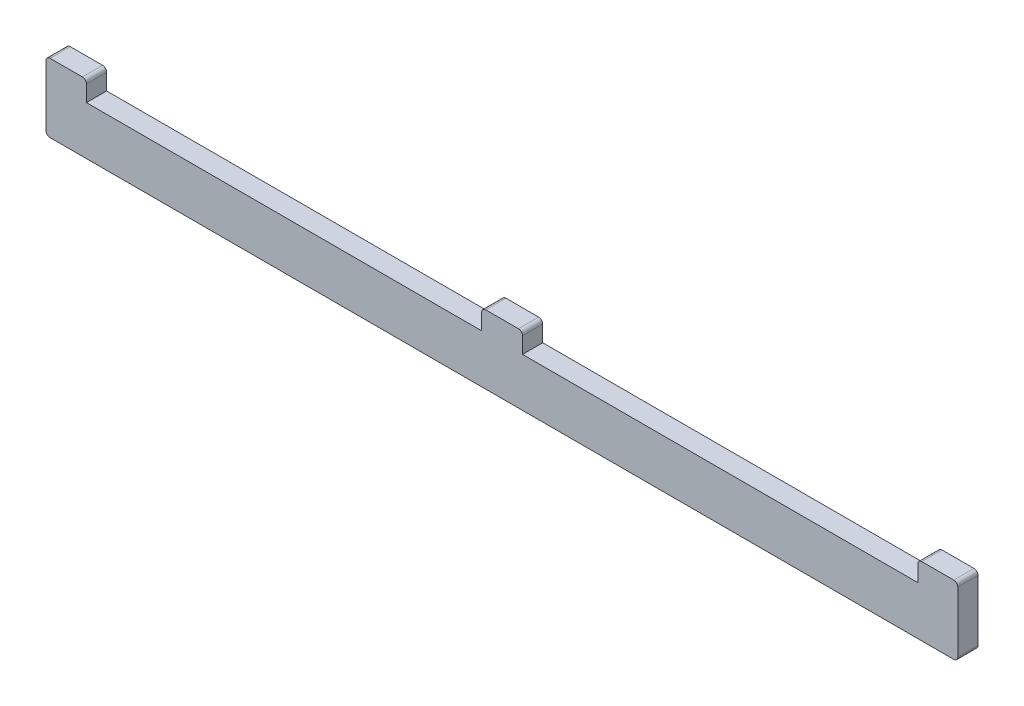
SolidWorks part; units mm, degrees
ref_plane "Front" through (0, 0, 0) normal (0, 0, 1) x (1, 0, 0)
ref_plane "Top" through (0, 0, 0) normal (0, 1, 0) x (1, 0, 0)
ref_plane "Right" through (0, 0, 0) normal (1, 0, 0) x (0, 0, -1)
sketch "Sketch1" plane through (0, 0, 0) normal (0, 0, 1) x (1, 0, 0)
  line L0 (117.9, 12) -> (215.7, 12)
  line L1 (1, 0) -> (224.6, 0)
  line L3 (10, 12) -> (107.8, 12)
  line L6 (107.8, 12) -> (107.8, 16)
  line L7 (108.8, 17) -> (116.9, 17)
  line L8 (117.9, 12) -> (117.9, 16)
  line L9 (225.6, 16) -> (225.6, 1)
  line L12 (1, 17) -> (9, 17)
  line L13 (10, 12) -> (10, 16)
  line L16 (224.6, 17) -> (216.7, 17)
  line L17 (215.7, 12) -> (215.7, 16)
  line L18 (0, 16) -> (0, 1)
  arc A0 (225.6, 1) -> (224.6, 0) centre (224.6, 1) cw
  arc A1 (1, 0) -> (0, 1) centre (1, 1) cw
  arc A2 (117.9, 16) -> (116.9, 17) centre (116.9, 16) ccw
  arc A3 (108.8, 17) -> (107.8, 16) centre (108.8, 16) ccw
  arc A4 (10, 16) -> (9, 17) centre (9, 16) ccw
  arc A5 (1, 17) -> (0, 16) centre (1, 16) ccw
  arc A6 (225.6, 16) -> (224.6, 17) centre (224.6, 16) ccw
  arc A7 (216.7, 17) -> (215.7, 16) centre (216.7, 16) ccw
  point P11 (225.6, 0)
  point P14 (0, 0)
  point P17 (117.9, 17)
  point P20 (107.8, 17)
  point P29 (10, 17)
  point P32 (-0.1, 17)
  point P35 (225.8, 17)
  point P38 (215.7, 17)
  dimension "D6" = 1
  dimension "D11" = 1
  dimension "D2" = 97.8
  dimension "D3" = 97.8
  dimension "D4" = 10.1
  dimension "D5" = 5
  dimension "D7" = 10.1
  dimension "D8" = 5
  dimension "D9" = 5
  dimension "D10" = 10.1
  dimension "D12" = 12
extrude "Boss-Extrude1" add sketch "Sketch1" along normal blind 5
